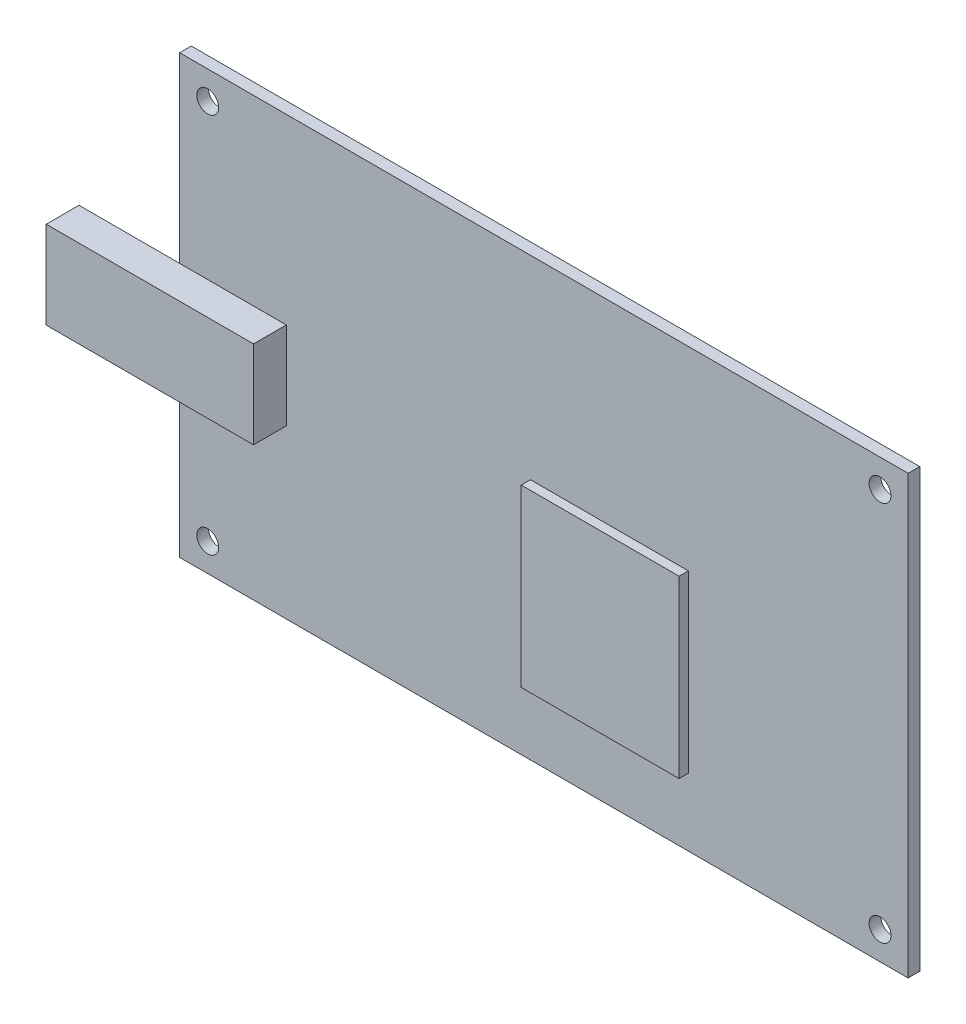
SolidWorks part; units mm, degrees
ref_plane "Front Plane" through (0, 0, 0) normal (0, 0, 1) x (1, 0, 0)
ref_plane "Top Plane" through (0, 0, 0) normal (0, 1, 0) x (1, 0, 0)
ref_plane "Right Plane" through (0, 0, 0) normal (1, 0, 0) x (0, 0, -1)
sketch "Sketch1" plane through (0, 0, 0) normal (0, 0, 1) x (1, 0, 0)
  line L1 (50, 30) -> (-50, 30)
  line L2 (50, 30) -> (50, -30)
  line L3 (50, -30) -> (-50, -30)
  line L4 (-50, 30) -> (-50, -30)
  line L5 (50, 30) -> (-50, -30) construction
  line L6 (50, -30) -> (-50, 30) construction
  point P0 (0, 0)
  dimension "D1" = 60
  dimension "D2" = 100
extrude "Boss-Extrude1" add sketch "Sketch1" along normal blind 1.6 contours L1 L4 L3 L2
sketch "Sketch2" plane through (0, 0, 1.6) normal (0, 0, 1) x (1, 0, 0)
  line L1 (-35.3639, 4.956) -> (-63.8158, 4.956)
  line L2 (-35.3639, 4.956) -> (-35.3639, -7.044)
  line L3 (-35.3639, -7.044) -> (-63.8158, -7.044)
  line L4 (-63.8158, 4.956) -> (-63.8158, -7.044)
  line L5 (-35.3639, 4.956) -> (-63.8158, -7.044) construction
  line L6 (-35.3639, -7.044) -> (-63.8158, 4.956) construction
  point P0 (-49.5899, -1.044)
  dimension "D1" = 28.4519
  dimension "D2" = 12
  dimension "D3" = 28.956
extrude "Boss-Extrude2" add sketch "Sketch2" along normal blind 4.5
sketch "Sketch3" plane through (0, 0, 1.6) normal (0, 0, 1) x (1, 0, 0)
  line L1 (19.8271, -20.7417) -> (-1.8409, -20.7417)
  line L2 (19.8271, -20.7417) -> (19.8271, 3.318)
  line L3 (19.8271, 3.318) -> (-1.8409, 3.318)
  line L4 (-1.8409, -20.7417) -> (-1.8409, 3.318)
  line L5 (19.8271, -20.7417) -> (-1.8409, 3.318) construction
  line L6 (19.8271, 3.318) -> (-1.8409, -20.7417) construction
  point P0 (8.9931, -8.7118)
extrude "Boss-Extrude3" add sketch "Sketch3" along normal blind 1.27
hole_wizard "Ø3.0 (3) Diameter Hole1" positions "Sketch4" profile "Sketch5" hole size "Ø3.0" standard "ANSI Metric"
sketch "Sketch4" plane through (0, 0, 1.6) normal (0, 0, 1) x (1, 0, 0)
  line L0 (50, -30) -> (-50, -30) construction
  line L1 (-50, -7.044) -> (-50, -30) construction
  line L2 (-50, 30) -> (-50, 4.956) construction
  line L3 (50, 30) -> (-50, 30) construction
  line L4 (50, 30) -> (50, -30) construction
  point P0 (-46.15, -26.15)
  point P2 (-46.15, 26.15)
  point P4 (46.15, -26.15)
  point P6 (46.15, 26.15)
  dimension "D1" = 3.85
  dimension "D2" = 3.85
  dimension "D3" = 3.85
  dimension "D4" = 3.85
  dimension "D5" = 3.85
  dimension "D6" = 3.85
  dimension "D7" = 3.85
  dimension "D8" = 3.85
sketch "Sketch5" plane through (-46.15, -26.15, 1.6) normal (1, 0, 0) x (0, -1, 0)
  line L0 (0, 0) -> (0, 4.0509)
  line L1 (0, 4.0509) -> (1.5, 3.1496)
  line L2 (1.5, 3.1496) -> (1.5, 0)
  line L5 (1.5, 0) -> (0, 0)
  line L10 (0, 4.0509) -> (-1.5, 3.1496) construction
  line L11 (0, -6.35) -> (0, 107.95) construction
  dimension "Hole Dia." = 3
  dimension "Hole Depth" = 3.1496
  dimension "Drill Angle" = 118
